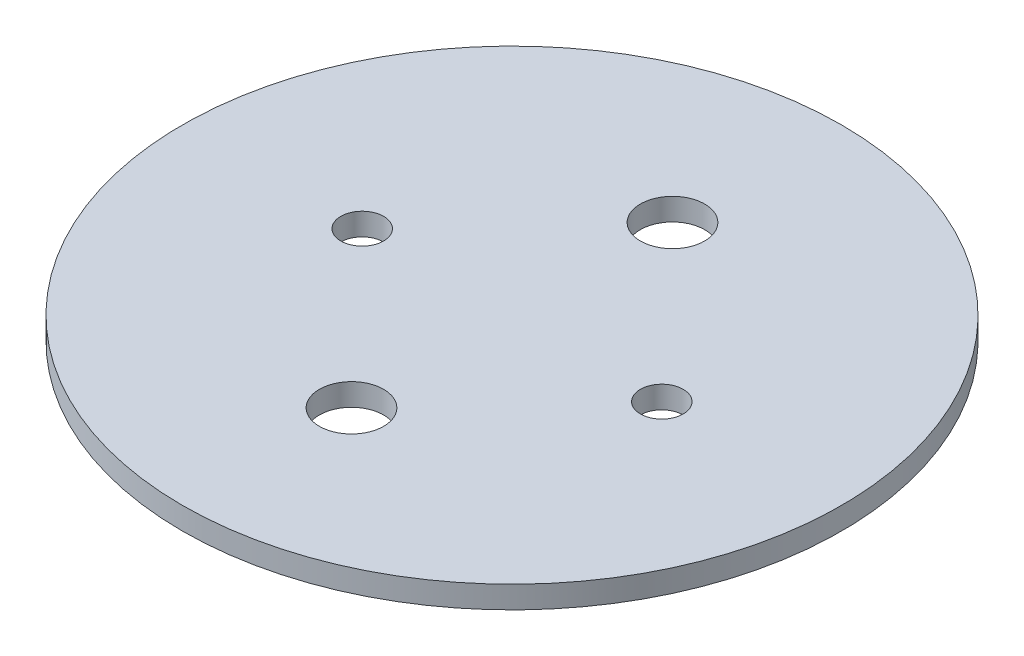
SolidWorks part; units mm, degrees
ref_plane "Front Plane" through (0, 0, 0) normal (0, 0, 1) x (1, 0, 0)
ref_plane "Top Plane" through (0, 0, 0) normal (0, 1, 0) x (1, 0, 0)
ref_plane "Right Plane" through (0, 0, 0) normal (1, 0, 0) x (0, 0, -1)
sketch "Sketch1" plane through (0, 0, 0) normal (0, 1, 0) x (1, 0, 0)
  line L0 (-22.225, 0) -> (22.225, 0) construction
  line L1 (0, 23.8125) -> (0, -23.8125) construction
  circle A0 centre (0, 0) radius 48.895
  circle A1 centre (22.225, 0) radius 3.175
  circle A2 centre (-22.225, 0) radius 3.175
  circle A3 centre (0, -23.8125) radius 4.7625
  circle A4 centre (0, 23.8125) radius 4.7625
  point P6 (0, 0)
  point P11 (0, 0)
  point P13 (0, 0)
  dimension "D1" = 6.35
  dimension "D2" = 97.79
  dimension "D5" = 47.625
  dimension "D4" = 9.525
  dimension "D3" = 44.45
extrude "Boss-Extrude1" add sketch "Sketch1" along normal blind 3.302
